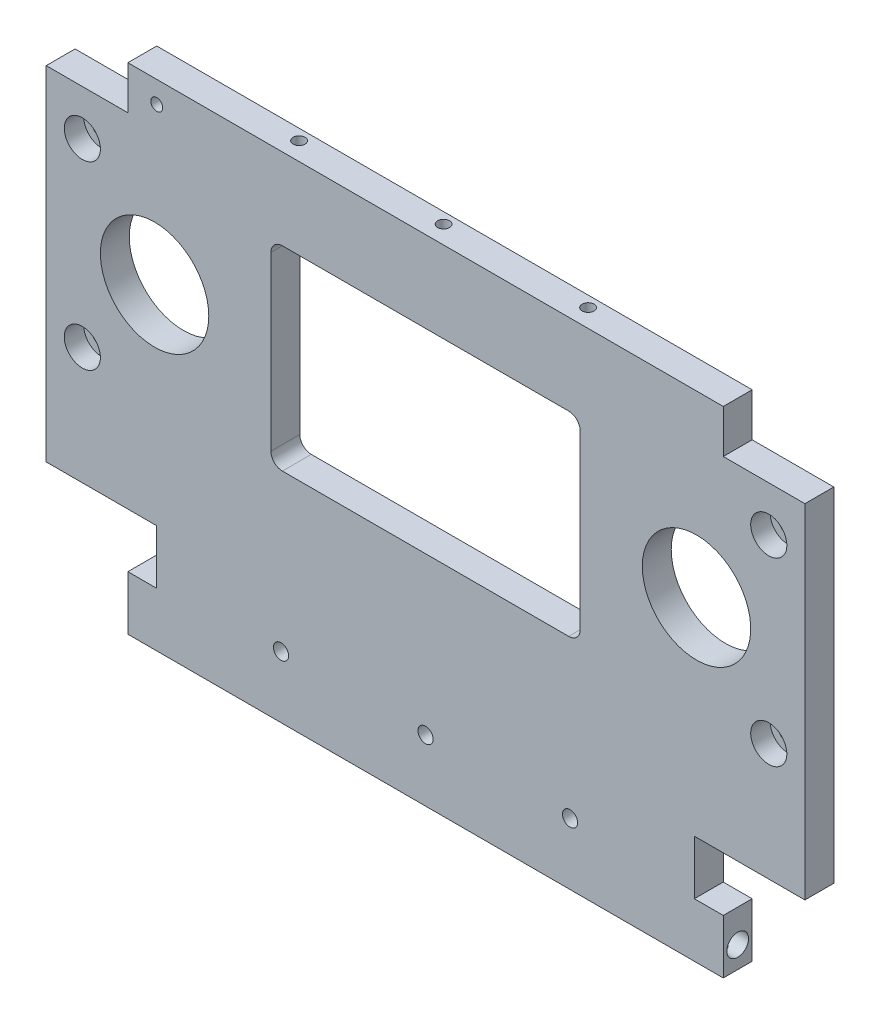
SolidWorks part; units mm, degrees
ref_plane "前视基准面" through (0, 0, 0) normal (0, 0, 1) x (1, 0, 0)
ref_plane "上视基准面" through (0, 0, 0) normal (0, 1, 0) x (1, 0, 0)
ref_plane "右视基准面" through (0, 0, 0) normal (1, 0, 0) x (0, 0, -1)
sketch "草图1" plane through (0, 0, 0) normal (0, 0, 1) x (1, 0, 0)
  line L1 (0, 0) -> (210, 0)
  line L2 (0, 0) -> (0, 75)
  line L3 (0, 75) -> (210, 75)
  line L4 (210, 0) -> (210, 75)
  dimension "D1" = 210
  dimension "D2" = 75
extrude "凸台-拉伸1" add sketch "草图1" along normal blind 8
sketch "草图2" plane through (0, 0, 8) normal (0, 0, 1) x (1, 0, 0)
  line L0 (210, 37.5) -> (0, 37.5) construction
  line L1 (210, 0) -> (210, 75) construction
  line L2 (0, 75) -> (0, 0) construction
  line L3 (0, 37.5) -> (105, 37.5) construction
  line L4 (105, 37.5) -> (105, -2.643) construction
  line L6 (144.62, 64.5) -> (65.38, 64.5)
  line L7 (147.8, 61.32) -> (147.8, 13.68)
  line L8 (144.62, 10.5) -> (65.38, 10.5)
  line L9 (62.2, 61.32) -> (62.2, 13.68)
  arc A0 (65.38, 10.5) -> (62.2, 13.68) centre (65.38, 13.68) cw
  arc A1 (62.2, 61.32) -> (65.38, 64.5) centre (65.38, 61.32) cw
  arc A2 (144.62, 10.5) -> (147.8, 13.68) centre (144.62, 13.68) ccw
  arc A3 (144.62, 64.5) -> (147.8, 61.32) centre (144.62, 61.32) cw
  point P16 (62.2, 64.5)
  point P19 (147.8, 10.5)
  point P22 (147.8, 64.5)
  dimension "D3" = 3.18
  dimension "D1" = 54
  dimension "D2" = 85.6
extrude "切除-拉伸1" cut sketch "草图2" against normal through all
hole_wizard "M5 六角凹头螺钉的柱形沉头孔1" positions "草图3" profile "草图4" counterbore size "M5" standard "ISO"
sketch "草图3" plane through (0, 0, 8) normal (0, 0, 1) x (1, 0, 0)
  line L0 (0, 37.5) -> (210, 37.5) construction
  line L1 (0, 75) -> (0, 0) construction
  line L2 (210, 0) -> (210, 75) construction
  line L3 (210, 37.5) -> (105, 37.5) construction
  line L4 (105, 37.5) -> (105, -47.7536) construction
  point P0 (10, 62.5)
  point P4 (10, 12.5)
  point P18 (200, 62.5)
  point P19 (200, 12.5)
  dimension "D1" = 50
  dimension "D2" = 10
sketch "草图4" plane through (10, 62.5, 8) normal (1, 0, 0) x (0, -1, 0)
  line L0 (0, 0) -> (0, 11.7524)
  line L1 (0, 11.7524) -> (2.75, 10.1)
  line L2 (2.75, 10.1) -> (2.75, 5.4)
  line L3 (2.75, 5.4) -> (5, 5.4)
  line L4 (5, 5.4) -> (5, 0)
  line L5 (5, 0) -> (0, 0)
  line L10 (0, 11.7524) -> (-2.75, 10.1) construction
  line L11 (0, -6.35) -> (0, 107.95) construction
  dimension "孔直径" = 5.5
  dimension "孔深度" = 10.1
  dimension "柱形沉头孔直径" = 10
  dimension "柱形沉头孔深度" = 5.4
  dimension "导头角度" = 118
sketch "草图5" plane through (0, 0, 8) normal (0, 0, 1) x (1, 0, 0)
  line L0 (0, 37.5) -> (210, 37.5) construction
  line L1 (0, 75) -> (0, 0) construction
  line L2 (210, 0) -> (210, 75) construction
  line L3 (210, 37.5) -> (105, 37.5) construction
  line L4 (105, 37.5) -> (105, 124.5038) construction
  circle A0 centre (30, 37.5) radius 15
  circle A1 centre (180, 37.5) radius 15
  dimension "D1" = 30
  dimension "D2" = 30
extrude "切除-拉伸2" cut sketch "草图5" against normal blind 13
sketch "草图6" plane through (0, 0, 0) normal (0, -1, 0) x (1, 0, 0)
  line L1 (0, 8) -> (210, 8)
  line L2 (0, 8) -> (0, 0)
  line L3 (0, 0) -> (210, 0)
  line L4 (210, 8) -> (210, 0)
extrude "凸台-拉伸2" add sketch "草图6" along normal blind 50
sketch "草图7" plane through (0, 0, 8) normal (0, 0, 1) x (1, 0, 0)
  line L0 (105, -50) -> (105, 47.0647) construction
  line L1 (0, -50) -> (22.6, -50)
  line L2 (0, -50) -> (0, -20)
  line L3 (0, -20) -> (22.6, -20)
  line L4 (22.6, -50) -> (22.6, -20)
  line L5 (210, -50) -> (0, -50) construction
  line L6 (210, -50) -> (210, -20)
  line L7 (210, -50) -> (187.4, -50)
  line L8 (187.4, -50) -> (187.4, -20)
  line L9 (210, -20) -> (187.4, -20)
  dimension "D1" = 30
  dimension "D2" = 22.6
extrude "切除-拉伸3" cut sketch "草图7" against normal blind 20
sketch "草图9" plane through (22.6, 0, 0) normal (-1, 0, 0) x (0, 0, 1)
  circle A0 centre (3.996, -44.028) radius 3
  dimension "D1" = 6
extrude "切除-拉伸5" cut sketch "草图9" against normal blind 8
ref_plane "基准面1" through (105, 0, 0) normal (-1, 0, 0) x (0, 0, 1)
mirror "镜向1" about plane through (105, 0, 0) normal (-1, 0, 0) of "切除-拉伸5"
ref_plane "基准面2" through (0, 27.5, 0) normal (0, 1, 0) x (1, 0, 0)
sketch "草图12" plane through (0, 75, 0) normal (0, 1, 0) x (1, 0, 0)
  line L0 (105, -8) -> (105, 0) construction
  line L1 (210, -8) -> (0, -8) construction
  line L2 (210, 0) -> (0, 0) construction
  line L4 (187.4, -8) -> (22.6, -8)
  line L5 (187.4, -8) -> (187.4, 0)
  line L6 (187.4, 0) -> (22.6, 0)
  line L7 (22.6, -8) -> (22.6, 0)
  dimension "D1" = 164.8
extrude "凸台-拉伸3" add sketch "草图12" along normal blind 12
sketch "草图13" plane through (0, 0, 8) normal (0, 0, 1) x (1, 0, 0)
  line L0 (105, -50) -> (105, 27.2823) construction
  line L1 (22.6, -20) -> (30.6, -20)
  line L2 (22.6, -20) -> (22.6, -35)
  line L3 (22.6, -35) -> (30.6, -35)
  line L4 (30.6, -20) -> (30.6, -35)
  line L5 (187.4, -50) -> (22.6, -50) construction
  line L6 (187.4, -20) -> (187.4, -35)
  line L7 (187.4, -35) -> (179.4, -35)
  line L8 (179.4, -20) -> (179.4, -35)
  line L9 (187.4, -20) -> (179.4, -20)
  dimension "D1" = 8
  dimension "D2" = 15
extrude "切除-拉伸6" cut sketch "草图13" against normal through all
hole_wizard "M4 螺纹孔1" positions "草图14" profile "草图15" tap size "M4" standard "ISO"
sketch "草图14" plane through (0, -50, 0) normal (0, -1, 0) x (-1, 0, 0)
  line L3 (-22.6, -4) -> (-187.4, -4) construction
  line L4 (-22.6, 0) -> (-22.6, -8) construction
  line L5 (-187.4, -8) -> (-187.4, 0) construction
  line L6 (-187.4, -4) -> (-105, -4) construction
  line L7 (-105, -4) -> (-105, -29.6967) construction
  point P0 (-27.6, -4.0022)
  point P20 (-182.4, -4.0022)
  dimension "D1" = 5
sketch "草图15" plane through (27.6, -50, 4.0022) normal (1, 0, 0) x (0, 0, -1)
  line L0 (0, 0) -> (0, 5.9914)
  line L1 (0, 5.9914) -> (1.65, 5)
  line L2 (1.65, 5) -> (1.65, 0)
  line L5 (1.65, 0) -> (0, 0)
  line L10 (0, 5.9914) -> (-1.65, 5) construction
  line L11 (0, -6.35) -> (0, 107.95) construction
  dimension "螺纹孔钻头直径" = 3.3
  dimension "螺纹孔钻头深度" = 5
  dimension "导头角度" = 118
cosmetic thread "孔螺蚊线1" parameters "D1"=3.4706, "D2"=4
cosmetic thread "孔螺蚊线2" parameters "D1"=3.4706, "D2"=4
hole_wizard "M4 螺纹孔2" positions "草图16" profile "草图17" tap size "M4" standard "ISO"
sketch "草图16" plane through (0, 0, 0) normal (0, 0, -1) x (-1, 0, 0)
  line L0 (-22.6, 87) -> (-22.6, 75) construction
  line L1 (-187.4, 87) -> (-22.6, 87) construction
  point P0 (-30.6, 81)
  dimension "D1" = 8
  dimension "D2" = 6
sketch "草图17" plane through (30.6, 81, 0) normal (1, 0, 0) x (0, 1, 0)
  line L0 (0, 0) -> (0, 11.0914)
  line L1 (0, 11.0914) -> (1.65, 10.1)
  line L2 (1.65, 10.1) -> (1.65, 0)
  line L5 (1.65, 0) -> (0, 0)
  line L10 (0, 11.0914) -> (-1.65, 10.1) construction
  line L11 (0, -6.35) -> (0, 107.95) construction
  dimension "螺纹孔钻头直径" = 3.3
  dimension "螺纹孔钻头深度" = 10.1
  dimension "导头角度" = 118
cosmetic thread "孔螺蚊线3" parameters "D1"=8, "D2"=4
hole_wizard "M5 螺纹孔1" positions "草图18" profile "草图19" tap size "M5" standard "ISO"
sketch "草图18" plane through (0, 0, 8) normal (0, 0, 1) x (1, 0, 0)
  point P0 (65, -32.943)
  point P3 (105, -32.943)
  point P6 (145, -32.943)
sketch "草图19" plane through (65, -32.943, 8) normal (1, 0, 0) x (0, -1, 0)
  line L0 (0, 0) -> (0, 9.2618)
  line L1 (0, 9.2618) -> (2.1, 8)
  line L2 (2.1, 8) -> (2.1, 0)
  line L5 (2.1, 0) -> (0, 0)
  line L10 (0, 9.2618) -> (-2.1, 8) construction
  line L11 (0, -6.35) -> (0, 107.95) construction
  dimension "螺纹孔钻头直径" = 4.2
  dimension "螺纹孔钻头深度" = 8
  dimension "导头角度" = 118
cosmetic thread "孔螺蚊线7" parameters "D1"=8, "D2"=5
cosmetic thread "孔螺蚊线8" parameters "D1"=8, "D2"=5
cosmetic thread "孔螺蚊线9" parameters "D1"=8, "D2"=5
hole_wizard "M4 螺纹孔3" positions "草图20" profile "草图21" tap size "M4" standard "ISO"
sketch "草图20" plane through (0, 87, 0) normal (0, 1, 0) x (1, 0, 0)
  point P0 (145, -3)
  point P3 (105, -3)
  point P6 (65, -3)
sketch "草图21" plane through (145, 87, 3) normal (1, 0, 0) x (0, 0, 1)
  line L0 (0, 0) -> (0, 6.9914)
  line L1 (0, 6.9914) -> (1.65, 6)
  line L2 (1.65, 6) -> (1.65, 0)
  line L5 (1.65, 0) -> (0, 0)
  line L10 (0, 6.9914) -> (-1.65, 6) construction
  line L11 (0, -6.35) -> (0, 107.95) construction
  dimension "螺纹孔钻头直径" = 3.3
  dimension "螺纹孔钻头深度" = 6
  dimension "导头角度" = 118
cosmetic thread "孔螺蚊线10" parameters "D1"=6, "D2"=4
cosmetic thread "孔螺蚊线11" parameters "D1"=6, "D2"=4
cosmetic thread "孔螺蚊线12" parameters "D1"=6, "D2"=4
